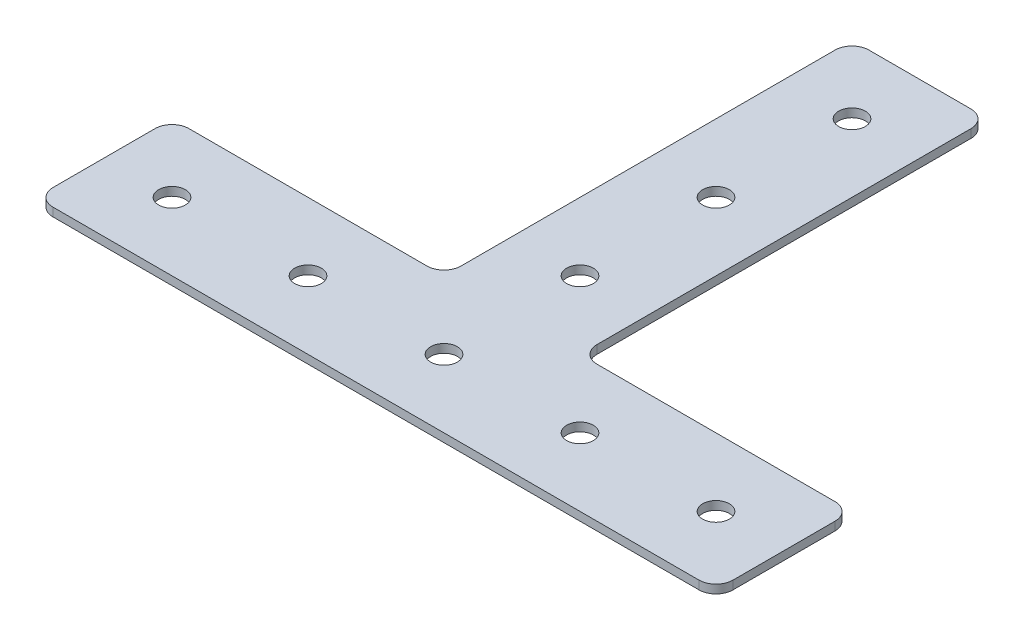
SolidWorks part; units mm, degrees
material "6061-T6 (SS)"
ref_plane "Front Plane" through (0, 0, 0) normal (0, 0, 1) x (1, 0, 0)
ref_plane "Top Plane" through (0, 0, 0) normal (0, 1, 0) x (1, 0, 0)
ref_plane "Right Plane" through (0, 0, 0) normal (1, 0, 0) x (0, 0, -1)
sketch "Sketch1" plane through (0, 0, 0) normal (0, 1, 0) x (1, 0, 0)
  line L0 (12.7, 12.7) -> (63.5, 12.7)
  line L1 (-63.5, -12.7) -> (63.5, -12.7)
  line L2 (-63.5, -12.7) -> (-63.5, 12.7)
  line L3 (-63.5, 12.7) -> (-12.7, 12.7)
  line L4 (63.5, -12.7) -> (63.5, 12.7)
  line L5 (-63.5, -12.7) -> (63.5, 12.7) construction
  line L6 (-63.5, 12.7) -> (63.5, -12.7) construction
  line L7 (-12.7, 88.9) -> (12.7, 88.9)
  line L8 (-12.7, 88.9) -> (-12.7, 12.7)
  line L10 (12.7, 88.9) -> (12.7, 12.7)
  point P0 (0, 0)
  dimension "D1" = 25.4
  dimension "D2" = 25.4
  dimension "D3" = 127
  dimension "D4" = 101.6
  dimension "D5" = 50.8
extrude "Boss-Extrude1" add sketch "Sketch1" along normal blind 1.5875
sketch "Sketch2" plane through (0, 1.5875, 0) normal (0, 1, 0) x (1, 0, 0)
  circle A0 centre (0, 0) radius 2.4892
  circle A1 centre (0, 25.4) radius 2.4892
  circle A2 centre (0, 50.8) radius 2.4892
  circle A3 centre (0, 76.2) radius 2.4892
  circle A4 centre (-25.4, 0) radius 2.4892
  circle A5 centre (-50.8, 0) radius 2.4892
  circle A6 centre (25.4, 0) radius 2.4892
  circle A7 centre (50.8, 0) radius 2.4892
  dimension "D1" = 4.9784
  dimension "D3" = 25.4
  dimension "D6" = 25.4
  dimension "D7" = 25.4
  dimension "D2" = 4
  dimension "D4" = 3
  dimension "D5" = 3
extrude "Cut-Extrude1" cut sketch "Sketch2" against normal through all and the other way through all
fillet "Fillet1" radius 3.175 8 edges at (63.5, 0.7937, 12.7) (-63.5, 0.7937, 12.7) (-12.7, 0.7937, -12.7) (-12.7, 0.7937, -88.9) (12.7, 0.7937, -88.9) (12.7, 0.7937, -12.7) (63.5, 0.7937, -12.7) (-63.5, 0.7937, -12.7)
